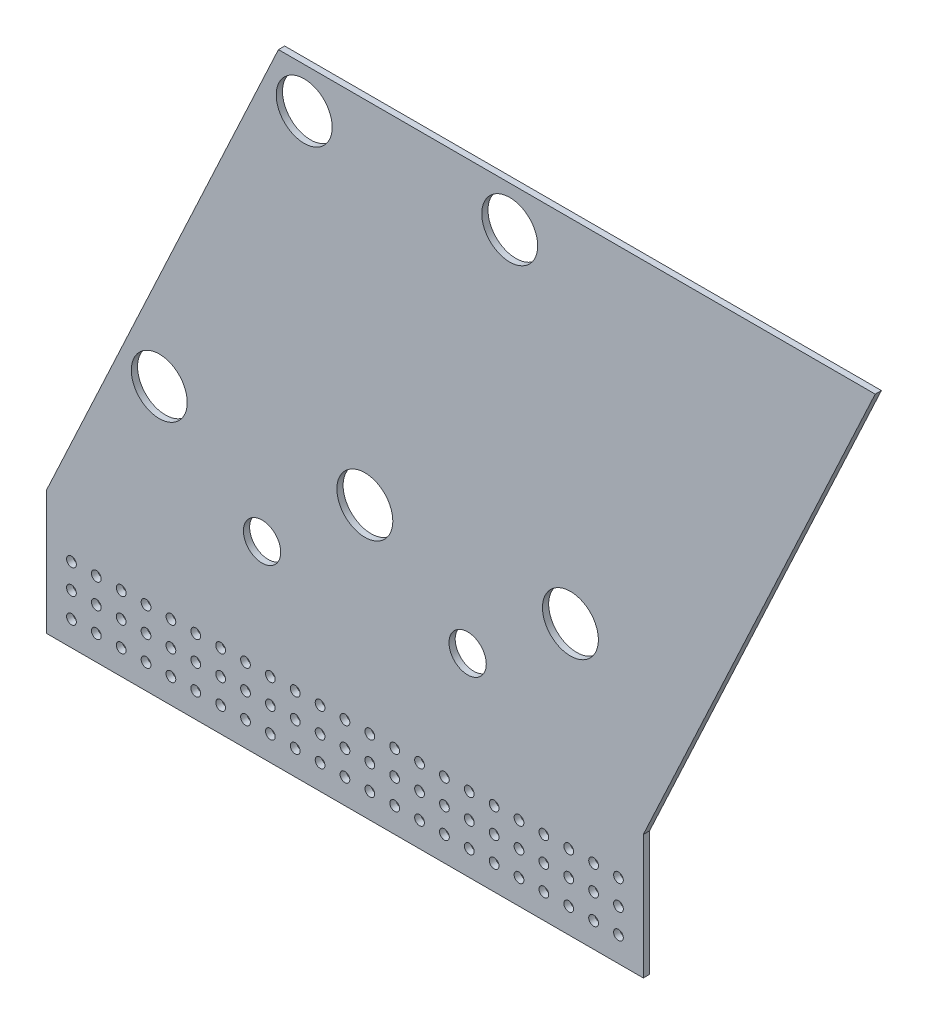
SolidWorks part; units mm, degrees
ref_plane "Front Plane" through (0, 0, 0) normal (0, 0, 1) x (1, 0, 0)
ref_plane "Top Plane" through (0, 0, 0) normal (0, 1, 0) x (1, 0, 0)
ref_plane "Right Plane" through (0, 0, 0) normal (1, 0, 0) x (0, 0, -1)
sketch "Sketch1" plane through (0, 0, 0) normal (0, 0, 1) x (1, 0, 0)
  line L0 (0, 0) -> (93.2732, 200.025)
  line L2 (93.2732, 200.025) -> (398.0732, 200.025)
  line L3 (398.0732, 200.025) -> (304.8, 0)
  line L4 (304.8, 0) -> (0, 0)
  line L6 (106.4207, 193.675) -> (106.4207, 200.025) construction
  line L8 (46.6366, 100.0125) -> (351.4366, 100.0125) construction
  line L9 (32.3944, 6.35) -> (32.3944, 0) construction
  line L10 (106.4207, 179.3875) -> (211.3989, 179.3875) construction
  line L11 (32.3944, 20.6375) -> (137.3944, 20.6375) construction
  line L12 (0, 0) -> (-25.169, -53.975)
  line L13 (-25.169, -53.975) -> (279.631, -53.975)
  line L14 (279.631, -53.975) -> (304.8, 0)
  line L15 (93.4719, 185.4257) -> (87.7168, 188.1093) construction
  line L16 (106.4207, 179.3875) -> (189.8944, -18.7467) construction
  line L17 (19.4455, 26.6757) -> (13.6905, 29.3593) construction
  line L18 (93.4719, 185.4257) -> (106.4207, 179.3875) construction
  line L19 (32.3944, 20.6375) -> (84.8944, -21.7889) construction
  line L20 (-25.169, -53.975) -> (-25.169, -117.475)
  line L21 (-25.169, -117.475) -> (279.631, -117.475)
  line L22 (279.631, -117.475) -> (279.631, -53.975)
  line L23 (-12.469, -79.375) -> (0.231, -79.375) construction
  line L24 (-12.469, -79.375) -> (-12.469, -92.075) construction
  line L25 (84.8944, 20.6375) -> (84.8944, -25.072) construction
  line L26 (137.3944, 20.6375) -> (242.3944, 20.6375) construction
  line L27 (189.8944, 20.6375) -> (189.8944, -150.5418) construction
  circle A0 centre (106.4207, 179.3875) radius 14.2875
  circle A2 centre (106.4207, 179.3875) radius 25.4 construction
  circle A3 centre (32.3944, 20.6375) radius 14.2875
  circle A4 centre (211.3989, 179.3875) radius 14.2875
  circle A5 centre (316.3771, 179.3875) radius 14.2875 construction
  circle A6 centre (137.3944, 20.6375) radius 14.2875
  circle A7 centre (242.3944, 20.6375) radius 14.2875
  circle A8 centre (84.8944, -21.7889) radius 9.525
  circle A9 centre (189.8944, -18.7467) radius 9.525
  circle A10 centre (32.3944, 20.6375) radius 25.4 construction
  circle A11 centre (-12.469, -79.375) radius 2.4892
  circle A12 centre (0.231, -79.375) radius 2.4892
  circle A13 centre (12.931, -79.375) radius 2.4892
  circle A14 centre (25.631, -79.375) radius 2.4892
  circle A15 centre (38.331, -79.375) radius 2.4892
  circle A16 centre (51.031, -79.375) radius 2.4892
  circle A17 centre (63.731, -79.375) radius 2.4892
  circle A18 centre (76.431, -79.375) radius 2.4892
  circle A19 centre (89.131, -79.375) radius 2.4892
  circle A20 centre (101.831, -79.375) radius 2.4892
  circle A21 centre (114.531, -79.375) radius 2.4892
  circle A22 centre (127.231, -79.375) radius 2.4892
  circle A23 centre (139.931, -79.375) radius 2.4892
  circle A24 centre (152.631, -79.375) radius 2.4892
  circle A25 centre (165.331, -79.375) radius 2.4892
  circle A26 centre (178.031, -79.375) radius 2.4892
  circle A27 centre (190.731, -79.375) radius 2.4892
  circle A28 centre (203.431, -79.375) radius 2.4892
  circle A29 centre (216.131, -79.375) radius 2.4892
  circle A30 centre (228.831, -79.375) radius 2.4892
  circle A31 centre (241.531, -79.375) radius 2.4892
  circle A32 centre (254.231, -79.375) radius 2.4892
  circle A33 centre (266.931, -79.375) radius 2.4892
  circle A34 centre (0.231, -92.075) radius 2.4892
  circle A35 centre (12.931, -92.075) radius 2.4892
  circle A36 centre (25.631, -92.075) radius 2.4892
  circle A37 centre (38.331, -92.075) radius 2.4892
  circle A38 centre (51.031, -92.075) radius 2.4892
  circle A39 centre (63.731, -92.075) radius 2.4892
  circle A40 centre (76.431, -92.075) radius 2.4892
  circle A41 centre (89.131, -92.075) radius 2.4892
  circle A42 centre (101.831, -92.075) radius 2.4892
  circle A43 centre (114.531, -92.075) radius 2.4892
  circle A44 centre (127.231, -92.075) radius 2.4892
  circle A45 centre (139.931, -92.075) radius 2.4892
  circle A46 centre (152.631, -92.075) radius 2.4892
  circle A47 centre (165.331, -92.075) radius 2.4892
  circle A48 centre (178.031, -92.075) radius 2.4892
  circle A49 centre (190.731, -92.075) radius 2.4892
  circle A50 centre (203.431, -92.075) radius 2.4892
  circle A51 centre (216.131, -92.075) radius 2.4892
  circle A52 centre (228.831, -92.075) radius 2.4892
  circle A53 centre (241.531, -92.075) radius 2.4892
  circle A54 centre (254.231, -92.075) radius 2.4892
  circle A55 centre (266.931, -92.075) radius 2.4892
  circle A56 centre (0.231, -104.775) radius 2.4892
  circle A57 centre (12.931, -104.775) radius 2.4892
  circle A58 centre (25.631, -104.775) radius 2.4892
  circle A59 centre (38.331, -104.775) radius 2.4892
  circle A60 centre (51.031, -104.775) radius 2.4892
  circle A61 centre (63.731, -104.775) radius 2.4892
  circle A62 centre (76.431, -104.775) radius 2.4892
  circle A63 centre (89.131, -104.775) radius 2.4892
  circle A64 centre (101.831, -104.775) radius 2.4892
  circle A65 centre (114.531, -104.775) radius 2.4892
  circle A66 centre (127.231, -104.775) radius 2.4892
  circle A67 centre (139.931, -104.775) radius 2.4892
  circle A68 centre (152.631, -104.775) radius 2.4892
  circle A69 centre (165.331, -104.775) radius 2.4892
  circle A70 centre (178.031, -104.775) radius 2.4892
  circle A71 centre (190.731, -104.775) radius 2.4892
  circle A72 centre (203.431, -104.775) radius 2.4892
  circle A73 centre (216.131, -104.775) radius 2.4892
  circle A74 centre (228.831, -104.775) radius 2.4892
  circle A75 centre (241.531, -104.775) radius 2.4892
  circle A76 centre (254.231, -104.775) radius 2.4892
  circle A77 centre (266.931, -104.775) radius 2.4892
  circle A78 centre (-12.469, -92.075) radius 2.4892
  circle A79 centre (-12.469, -104.775) radius 2.4892
  circle A80 centre (84.8944, -21.7889) radius 31.75 construction
  circle A81 centre (137.3944, 20.6375) radius 25.4 construction
  circle A82 centre (189.8944, -18.7467) radius 31.75 construction
  dimension "D1" = 304.8
  dimension "D2" = 28.575
  dimension "D3" = 50.8
  dimension "D5" = 6.35
  dimension "D15" = 19.05
  dimension "D11" = 67.5
  dimension "D20" = 63.5
  dimension "D21" = 25.4
  dimension "D23" = 4.9784
  dimension "D16" = 63.5
  dimension "D4" = 6.35
  dimension "D6" = 158.75
  dimension "D7" = 6.35
  dimension "D8" = 3
  dimension "D9" = 104.9782
  dimension "D10" = 115
  dimension "D13" = 105
  dimension "D14" = 53.975
  dimension "D18" = 215
  dimension "D19" = 6.35
  dimension "D22" = 12.7
  dimension "D26" = 90
  dimension "D27" = 12.7
  dimension "D28" = 12.7
  dimension "D12" = 3
  dimension "D24" = 23
  dimension "D25" = 3
extrude "Boss-Extrude3" add sketch "Sketch1" along normal blind 3.175 contours L4 L3 L2 L0 A7 A6 A5 A4 A3 A0 | L13 L14 L4 L12 | L21 L22 L13 L20 A79 A78 A77 A76 A75 A74 A73 A72 A71 A70 A69 A68 A67 A66 A65 A64 A63 A62 A61 A60 A59 A58 A57
ref_plane "Plane1" through (0, 0, -60.325) normal (0, 0, -1) x (-1, 0, 0)
sketch "Sketch2" plane through (0, 0, 3.175) normal (0, 0, 1) x (1, 0, 0)
  line L0 (137.3944, 20.6375) -> (32.3944, 20.6375) construction
  line L3 (69.6544, 105.0925) -> (89.9744, 105.0925)
  line L4 (69.6544, 105.0925) -> (69.6544, 94.9325)
  line L5 (69.6544, 94.9325) -> (89.9744, 94.9325)
  line L6 (89.9744, 105.0925) -> (89.9744, 94.9325)
  line L7 (84.8944, 20.6375) -> (84.8944, 149.223) construction
  circle A0 centre (137.3944, 20.6375) radius 14.2875 construction
  circle A2 centre (74.7344, 100.0125) radius 1.5875
  circle A3 centre (84.8944, 100.0125) radius 2.7781
  point P8 (69.6544, 100.0125)
  point P17 (0, 0)
  dimension "D3" = 79.375
  dimension "D4" = 3.175
  dimension "D5" = 5.5562
  dimension "D1" = 20.32
  dimension "D2" = 10.16
  dimension "D6" = 5.08
  dimension "D7" = 5.08
